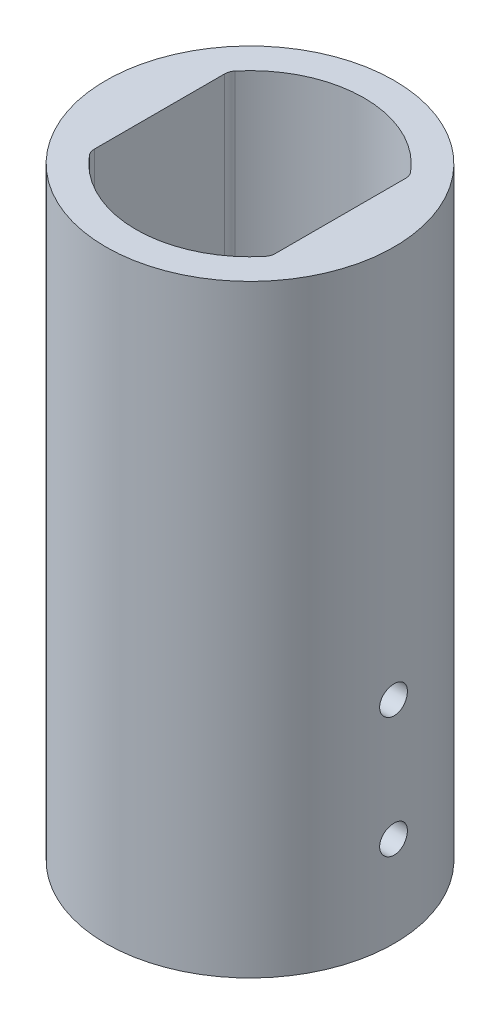
SolidWorks part; units mm, degrees
ref_plane "Front Plane" through (0, 0, 0) normal (0, 0, 1) x (1, 0, 0)
ref_plane "Top Plane" through (0, 0, 0) normal (0, 1, 0) x (1, 0, 0)
ref_plane "Right Plane" through (0, 0, 0) normal (1, 0, 0) x (0, 0, -1)
sketch "Sketch1" plane through (0, 0, 0) normal (0, 1, 0) x (1, 0, 0)
  line L0 (-15, 11.4983) -> (-15, -11.4983)
  line L1 (15, 11.4983) -> (15, -11.4983)
  circle A0 centre (0, 0) radius 23.9
  circle A1 centre (0, 0) radius 18.9
  dimension "D1" = 47.8
  dimension "D2" = 37.8
  dimension "D3" = 15
  dimension "D4" = 15
extrude "Boss-Extrude1" add sketch "Sketch1" along normal blind 100 contours A0 A1 | L0 A1 | L1 A1
sketch "Sketch2" plane through (0, 0, 0) normal (1, 0, 0) x (0, 0, -1)
  circle A0 centre (0, 15) radius 2.3
  circle A1 centre (0, 35) radius 2.3
  dimension "D3" = 15
  dimension "D1" = 4.6
  dimension "D2" = 4.6
  dimension "D4" = 20
extrude "Cut-Extrude1" cut sketch "Sketch2" against normal through all both and the other way through all
fillet "Fillet1" radius 2 4 edges at (-15, 50, -11.4983) (-15, 50, 11.4983) (15, 50, 11.4983) (15, 50, -11.4983)
equation "\"D1@Sketch1\"=\"TubeInnerDiameter\""
equation "\"TubeInnerDiameter\"= 47.8"
equation "\"ReleaseMechanisumHeight\"=100"
equation "\"WireDiameter\"=3.38983"
equation "\"servoHoleDiameter\" = 2.8"
equation "\"CordDiameter\"= 5"
equation "\"MountingBoldDiameter\"=2.8"
equation "\"D2@Sketch1\"=\"TubeInnerDiameter\"-10"
equation "\"D1@Boss-Extrude1\"=\"ReleaseMechanisumHeight\""
equation "\"TubeMountingBoltDiameter\" = 5"
equation "\"D1@Sketch2\"=\"TubeMountingBoltDiameter\"-0.4"
equation "\"D2@Sketch2\"=\"TubeMountingBoltDiameter\"-0.4"
